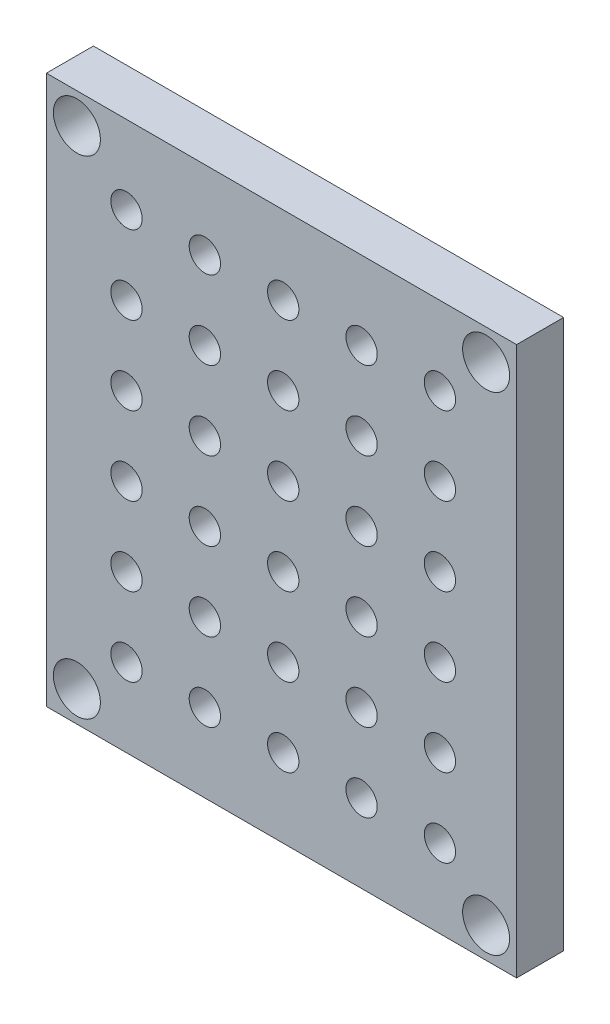
SolidWorks part; units mm, degrees
ref_plane "Plan de face" through (0, 0, 0) normal (0, 0, 1) x (1, 0, 0)
ref_plane "Plan de dessus" through (0, 0, 0) normal (0, 1, 0) x (1, 0, 0)
ref_plane "Plan de droite" through (0, 0, 0) normal (1, 0, 0) x (0, 0, -1)
sketch "Esquisse2" plane through (0, 0, 0) normal (0, 0, 1) x (1, 0, 0)
  line L1 (-10, 15.5) -> (10, 15.5)
  line L2 (13, 12.5) -> (13, -12.5)
  line L4 (10, -15.5) -> (-10, -15.5)
  line L8 (-10, 15.5) -> (-13, 12.5)
  line L9 (-13, -12.5) -> (-10, -15.5)
  line L10 (10, -15.5) -> (13, -12.5)
  line L11 (10, 15.5) -> (13, 12.5)
  line L12 (-13, -12.5) -> (-13, 12.5)
  dimension "D2" = 13
  dimension "D3" = 15.5
  dimension "D4" = 15.5
  dimension "D5" = 3
  dimension "D6" = 3
  dimension "D7" = 3
  dimension "D8" = 3
  dimension "D9" = 3
  dimension "D10" = 3
  dimension "D11" = 3
  dimension "D12" = 3
  dimension "D13" = 26
sketch "Esquisse8" plane through (0, 0, 0) normal (0, 0, 1) x (1, 0, 0)
  line L0 (-9.5, 15) -> (9.5, 15)
  line L1 (9.5, 15) -> (12.5, 12)
  line L2 (12.5, 12) -> (12.5, -12)
  line L3 (12.5, -12) -> (9.5, -15)
  line L4 (9.5, -15) -> (-9.5, -15)
  line L5 (-10, 15.5) -> (10, 15.5) construction
  line L6 (-13, -12.5) -> (-13, 12.5) construction
  line L7 (-9.5, -15) -> (-12.5, -12)
  line L8 (-12.5, -12) -> (-12.5, 12)
  line L10 (10, -15.5) -> (-10, -15.5) construction
  line L11 (-12.5, 12) -> (-9.5, 15)
  point P4 (-12.5, 0)
  point P5 (12.5, 0)
  point P6 (0, 15)
  point P8 (0, -15)
  dimension "D1" = 0.5
  dimension "D2" = 0.5
  dimension "D3" = 3
  dimension "D4" = 3
  dimension "D5" = 0.5
extrude "Boss.-Extru.4" add sketch "Esquisse8" against normal blind 2 separate body
sketch "Esquisse9" plane through (0, 0, 0) normal (0, 0, 1) x (1, 0, 0)
  line L1 (-15, 17.5) -> (15, 17.5)
  line L2 (-15, 17.5) -> (-15, -17.5)
  line L3 (-15, -17.5) -> (15, -17.5)
  line L4 (15, 17.5) -> (15, -17.5)
  dimension "D1" = 30
  dimension "D2" = 35
extrude "Boss.-Extru.5" add sketch "Esquisse9" along normal blind 3
sketch "Esquisse7" plane through (0, 0, 3) normal (0, 0, 1) x (1, 0, 0)
  line L0 (-15, 17.5) -> (-11.5, 14) construction
  line L2 (15, 17.5) -> (11.5, 14) construction
  line L4 (11.5, -14) -> (15, -17.5) construction
  line L6 (-11.5, -14) -> (-15, -17.5) construction
  line L8 (-10, 15.5) -> (-13, 12.5) construction
  line L9 (15, 17.5) -> (-15, 17.5) construction
  line L10 (15, -17.5) -> (15, 17.5) construction
  line L11 (10, 15.5) -> (13, 12.5) construction
  line L12 (-13, -12.5) -> (-10, -15.5) construction
  line L13 (10, -15.5) -> (13, -12.5) construction
  circle A0 centre (-13.0555, 15.5555) radius 1.5
  circle A1 centre (-13.0555, -15.5555) radius 1.5
  circle A2 centre (13.0555, -15.5555) radius 1.5
  circle A3 centre (13.0555, 15.5555) radius 1.5
  dimension "D1" = 3
  dimension "D3" = 2.75
  dimension "D2" = 2.75
  dimension "D4" = 2.75
  dimension "D5" = 2.75
extrude "Enlèv. mat.-Extru.8" cut sketch "Esquisse7" against normal through all
sketch "Esquisse10" plane through (0, 0, 3) normal (0, 0, 1) x (1, 0, 0)
  circle A0 centre (-9.8903, 12.5067) radius 1
  circle A1 centre (-4.8903, 12.5067) radius 1
  circle A2 centre (0.1097, 12.5067) radius 1
  circle A3 centre (5.1097, 12.5067) radius 1
  circle A4 centre (10.1097, 12.5067) radius 1
  circle A5 centre (-4.8903, 7.5067) radius 1
  circle A6 centre (0.1097, 7.5067) radius 1
  circle A7 centre (5.1097, 7.5067) radius 1
  circle A8 centre (10.1097, 7.5067) radius 1
  circle A9 centre (-4.8903, 2.5067) radius 1
  circle A10 centre (0.1097, 2.5067) radius 1
  circle A11 centre (5.1097, 2.5067) radius 1
  circle A12 centre (10.1097, 2.5067) radius 1
  circle A13 centre (-4.8903, -2.4933) radius 1
  circle A14 centre (0.1097, -2.4933) radius 1
  circle A15 centre (5.1097, -2.4933) radius 1
  circle A16 centre (10.1097, -2.4933) radius 1
  circle A17 centre (-4.8903, -7.4933) radius 1
  circle A18 centre (0.1097, -7.4933) radius 1
  circle A19 centre (5.1097, -7.4933) radius 1
  circle A20 centre (10.1097, -7.4933) radius 1
  circle A21 centre (-4.8903, -12.4933) radius 1
  circle A22 centre (0.1097, -12.4933) radius 1
  circle A23 centre (5.1097, -12.4933) radius 1
  circle A24 centre (10.1097, -12.4933) radius 1
  circle A25 centre (-9.8903, 7.5067) radius 1
  circle A26 centre (-9.8903, 2.5067) radius 1
  circle A27 centre (-9.8903, -2.4933) radius 1
  circle A28 centre (-9.8903, -7.4933) radius 1
  circle A29 centre (-9.8903, -12.4933) radius 1
  dimension "D1" = 2
extrude "Enlèv. mat.-Extru.9" cut sketch "Esquisse10" against normal through all
